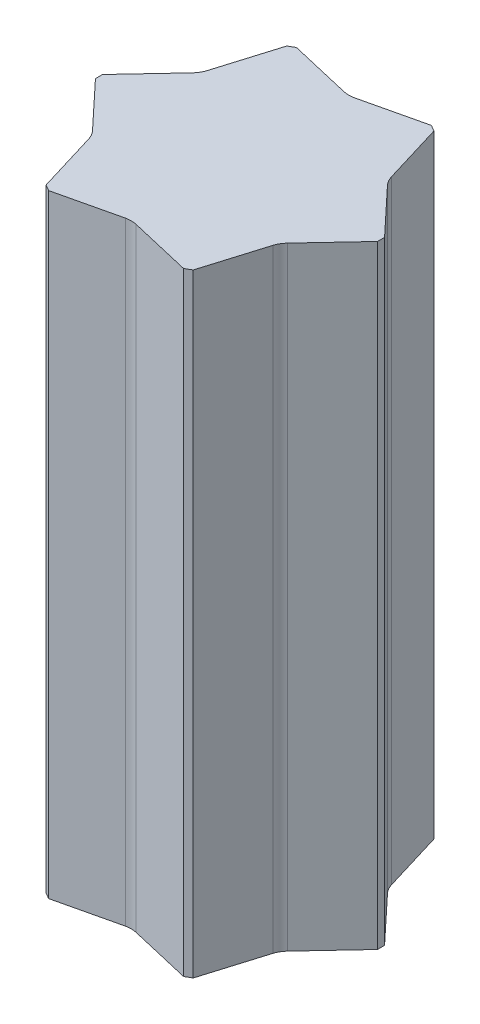
SolidWorks part; units mm, degrees
material "PEN"
ref_plane "前视基准面" through (0, 0, 0) normal (0, 0, 1) x (1, 0, 0)
ref_plane "上视基准面" through (0, 0, 0) normal (0, 1, 0) x (1, 0, 0)
ref_plane "右视基准面" through (0, 0, 0) normal (1, 0, 0) x (0, 0, -1)
sketch "草图2" plane through (0, 0, 0) normal (0, 1, 0) x (1, 0, 0)
  line L1 (345, 8.6603) -> (180, 294.4486)
  line L2 (165, 303.1089) -> (-165, 303.1089)
  line L3 (-180, 294.4486) -> (-345, 8.6603)
  line L4 (-345, -8.6603) -> (-180, -294.4486)
  line L5 (-165, -303.1089) -> (165, -303.1089)
  line L6 (180, -294.4486) -> (345, -8.6603)
  line L8 (-180, 294.4486) -> (-165, 303.1089)
  line L19 (165, 303.1089) -> (180, 294.4486)
  line L20 (345, 8.6603) -> (345, -8.6603)
  line L21 (165, -303.1089) -> (180, -294.4486)
  line L22 (-180, -294.4486) -> (-165, -303.1089)
  line L23 (-345, 8.6603) -> (-345, -8.6603)
  circle A0 centre (0, 0) radius 303.1089 construction
extrude "凸台-拉伸1" add sketch "草图2" along normal blind 1500
sketch "草图4" plane through (0, 0, 0) normal (0, 1, 0) x (1, 0, 0)
  line L0 (-165, 323.1172) -> (-165, 283.3064)
  line L1 (165, 303.1089) -> (-165, 303.1089) construction
  line L9 (165, 303.1089) -> (165, 323.0131)
  line L10 (165, 303.1089) -> (165, 283.2046)
  line L15 (-12.996, 247.6102) -> (-165, 283.3064)
  line L16 (-165, 323.1172) -> (-12.996, 358.6076)
  line L17 (12.996, 358.6076) -> (165, 323.0131)
  line L18 (165, 283.2046) -> (12.996, 247.6102)
  arc A3 (-12.996, 358.6076) -> (12.996, 358.6076) centre (0, 303.1089) cw
  arc A4 (12.996, 247.6102) -> (-12.996, 247.6102) centre (0, 303.1089) cw
sketch "草图5" plane through (0, 0, 0) normal (0, 1, 0) x (1, 0, 0)
  line L36 (238.2174, 122.5284) -> (345, 8.6603)
  line L37 (225.2214, 145.0381) -> (180, 294.4486)
  line L38 (180, 294.4486) -> (214.9693, 314.6382)
  line L39 (321.3479, 200.5368) -> (214.9693, 314.6382)
  line L40 (334.3439, 178.0271) -> (379.5202, 28.5905)
  line L41 (379.5202, 28.5905) -> (345, 8.6603)
  line L42 (225.2214, -145.0381) -> (180, -294.4486)
  line L43 (238.2174, -122.5284) -> (345, -8.6603)
  line L44 (12.996, 267.5665) -> (165, 303.1089)
  line L45 (-12.996, 267.5665) -> (-165, 303.1089)
  line L46 (-12.996, 378.5639) -> (-165, 343.488)
  line L47 (12.996, 378.5639) -> (165, 342.9694)
  line L48 (165, 342.9694) -> (165, 303.1089)
  line L49 (-165, 303.1089) -> (-165, 343.488)
  line L50 (345, -8.6603) -> (379.9693, -28.8498)
  line L51 (334.3439, -178.0271) -> (379.9693, -28.8498)
  line L52 (321.3479, -200.5368) -> (214.5202, -314.3789)
  line L53 (214.5202, -314.3789) -> (180, -294.4486)
  line L54 (-12.996, -267.5665) -> (-165, -303.1089)
  line L55 (12.996, -267.5665) -> (165, -303.1089)
  line L56 (165, -303.1089) -> (165, -343.488)
  line L57 (12.996, -378.5639) -> (165, -343.488)
  line L58 (-12.996, -378.5639) -> (-165, -342.9694)
  line L59 (-165, -342.9694) -> (-165, -303.1089)
  line L60 (-238.2174, -122.5284) -> (-345, -8.6603)
  line L61 (-225.2214, -145.0381) -> (-180, -294.4486)
  line L62 (-180, -294.4486) -> (-214.9693, -314.6382)
  line L63 (-321.3479, -200.5368) -> (-214.9693, -314.6382)
  line L64 (-334.3439, -178.0271) -> (-379.5202, -28.5905)
  line L65 (-379.5202, -28.5905) -> (-345, -8.6603)
  line L66 (-225.2214, 145.0381) -> (-180, 294.4486)
  line L67 (-238.2174, 122.5284) -> (-345, 8.6603)
  line L68 (-345, 8.6603) -> (-379.9693, 28.8498)
  line L69 (-334.3439, 178.0271) -> (-379.9693, 28.8498)
  line L70 (-321.3479, 200.5368) -> (-214.5202, 314.3789)
  line L71 (-214.5202, 314.3789) -> (-180, 294.4486)
  arc A13 (-12.996, 378.5639) -> (12.996, 378.5639) centre (0, 323.0652) cw
  arc A14 (-12.996, 267.5665) -> (12.996, 267.5665) centre (0, 323.0652) ccw
  arc A15 (225.2214, 145.0381) -> (238.2174, 122.5284) centre (279.7826, 161.5326) ccw
  arc A16 (321.3479, 200.5368) -> (334.3439, 178.0271) centre (279.7826, 161.5326) cw
  arc A17 (238.2174, -122.5284) -> (225.2214, -145.0381) centre (279.7826, -161.5326) ccw
  arc A18 (334.3439, -178.0271) -> (321.3479, -200.5368) centre (279.7826, -161.5326) cw
  arc A19 (12.996, -267.5665) -> (-12.996, -267.5665) centre (0, -323.0652) ccw
  arc A20 (12.996, -378.5639) -> (-12.996, -378.5639) centre (0, -323.0652) cw
  arc A21 (-225.2214, -145.0381) -> (-238.2174, -122.5284) centre (-279.7826, -161.5326) ccw
  arc A22 (-321.3479, -200.5368) -> (-334.3439, -178.0271) centre (-279.7826, -161.5326) cw
  arc A23 (-238.2174, 122.5284) -> (-225.2214, 145.0381) centre (-279.7826, 161.5326) ccw
  arc A24 (-334.3439, 178.0271) -> (-321.3479, 200.5368) centre (-279.7826, 161.5326) cw
  dimension "D1" = 6
extrude "切除-拉伸4" cut sketch "草图5" along normal blind 1500
